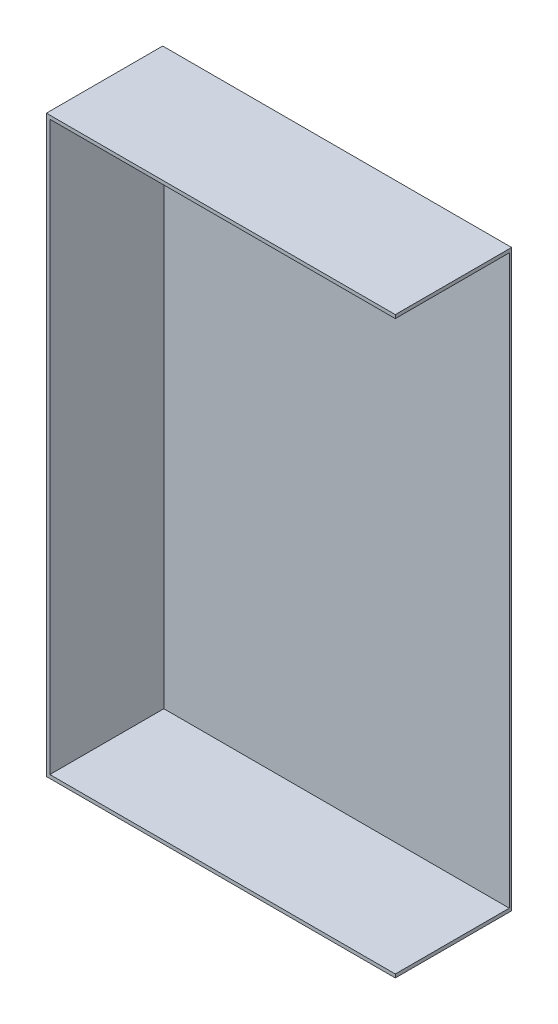
SolidWorks part; units mm, degrees
material "Acrylic (Medium-high impact)"
ref_plane "Front Plane" through (0, 0, 0) normal (0, 0, 1) x (1, 0, 0)
ref_plane "Top Plane" through (0, 0, 0) normal (0, 1, 0) x (1, 0, 0)
ref_plane "Right Plane" through (0, 0, 0) normal (1, 0, 0) x (0, 0, -1)
sketch "Sketch1" plane through (0, 0, 0) normal (0, 0, 1) x (1, 0, 0)
  line L1 (0, 0) -> (381, 0)
  line L2 (0, 0) -> (0, 627.38)
  line L3 (0, 627.38) -> (381, 627.38)
  line L4 (381, 0) -> (381, 627.38)
  dimension "D1" = 627.38
  dimension "D2" = 381
extrude "Boss-Extrude1" add sketch "Sketch1" along normal blind 127
sketch "Sketch2" plane through (0, 0, 127) normal (0, 0, 1) x (1, 0, 0)
  line L0 (381, 0) -> (381, 627.38) construction
  line L1 (381, 623.57) -> (3.81, 623.57)
  line L2 (381, 623.57) -> (381, 3.81)
  line L3 (381, 3.81) -> (3.81, 3.81)
  line L4 (3.81, 623.57) -> (3.81, 3.81)
  line L5 (0, 627.38) -> (0, 0) construction
  line L6 (381, 627.38) -> (0, 627.38) construction
  line L7 (0, 0) -> (381, 0) construction
  dimension "D1" = 3.81
  dimension "D2" = 3.81
  dimension "D3" = 3.81
extrude "Cut-Extrude1" cut sketch "Sketch2" against normal offset from surface (124.46 mm away) 2.54 up to face at (190.5, 313.69, 0)
equation "\"wall thickness\"= .15"
equation "\"floor thickness\"= .10"
equation "\"D1@Sketch2\"=\"wall thickness\""
equation "\"D2@Sketch2\"=\"wall thickness\""
equation "\"D3@Sketch2\"=\"wall thickness\""
equation "\"D1@Cut-Extrude1\"=\"floor thickness\""
